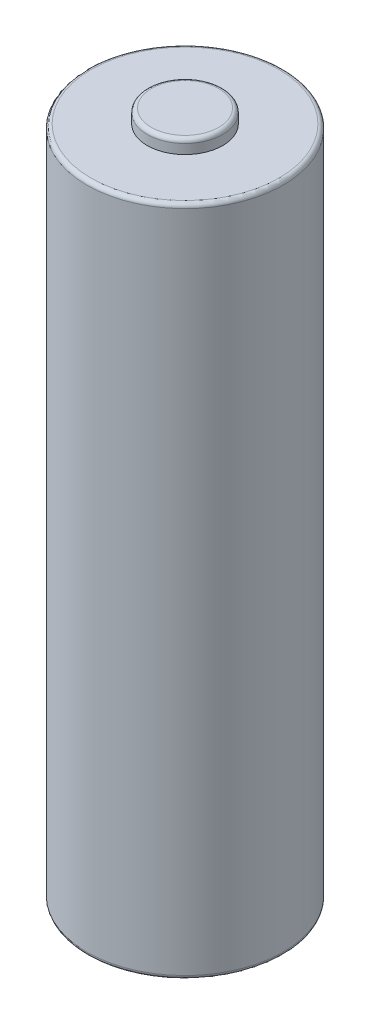
SolidWorks part; units mm, degrees
ref_plane "Front Plane" through (0, 0, 0) normal (0, 0, 1) x (1, 0, 0)
ref_plane "Top Plane" through (0, 0, 0) normal (0, 1, 0) x (1, 0, 0)
ref_plane "Right Plane" through (0, 0, 0) normal (1, 0, 0) x (0, 0, -1)
sketch "Sketch1" plane through (0, 0, 0) normal (0, 1, 0) x (1, 0, 0)
  circle A0 centre (0, 0) radius 7.15
  dimension "D1" = 14.3
extrude "Boss-Extrude1" add sketch "Sketch1" along normal blind 49
sketch "Sketch2" plane through (0, 49, 0) normal (0, 1, 0) x (1, 0, 0)
  circle A0 centre (0, 0) radius 2.75
  dimension "D1" = 5.5
extrude "Boss-Extrude2" add sketch "Sketch2" along normal blind 1
fillet "Fillet1" radius 0.3 3 edges at (0, 0, 7.15) (0, 49, 7.15) (0, 50, 2.75)
sketch "Sketch3" plane through (0, 0, 0) normal (0, -1, 0) x (1, 0, 0)
  circle A0 centre (0, 0) radius 5
  dimension "D1" = 10
extrude "Boss-Extrude3" add sketch "Sketch3" along normal blind 1
fillet "Fillet3" radius 0.1 1 edges at (0, -1, -5)
